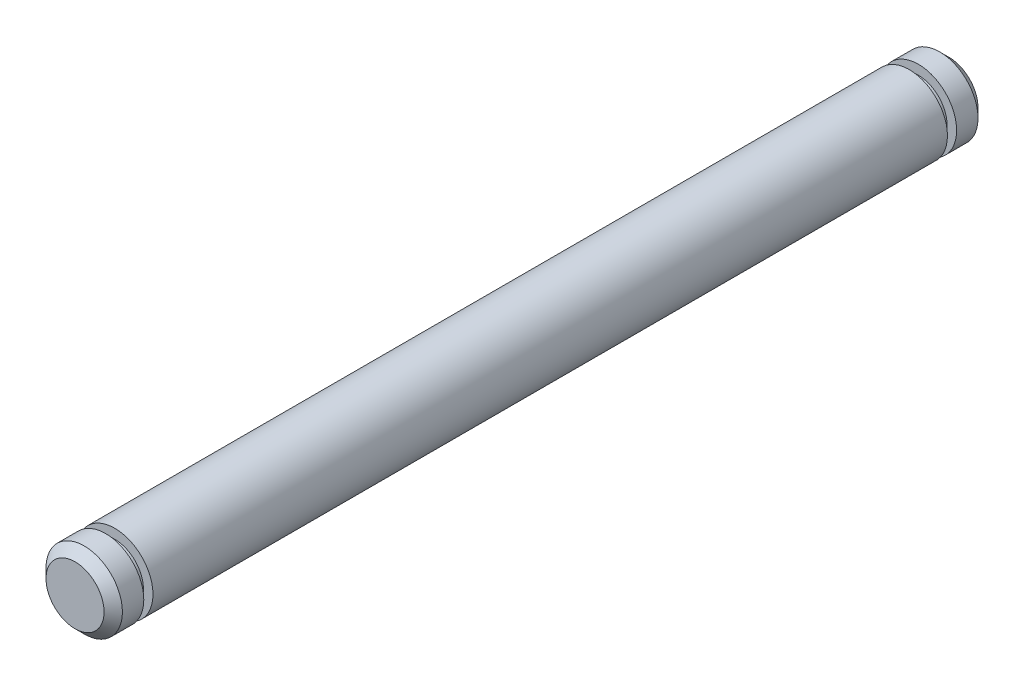
SolidWorks part; units mm, degrees
ref_plane "Front Plane" through (0, 0, 0) normal (0, 0, 1) x (1, 0, 0)
ref_plane "Top Plane" through (0, 0, 0) normal (0, 1, 0) x (1, 0, 0)
ref_plane "Right Plane" through (0, 0, 0) normal (1, 0, 0) x (0, 0, -1)
sketch "Sketch1" plane through (0, 0, 0) normal (0, 0, 1) x (1, 0, 0)
  circle A0 centre (0, 0) radius 1.5875
  dimension "D1" = 3.175
extrude "Boss-Extrude1" add sketch "Sketch1" along normal mid plane 33.0149
sketch "Sketch2" plane through (0, 0, 16.5075) normal (0, 0, 1) x (1, 0, 0)
  circle A0 centre (0, 0) radius 1.1913
  dimension "D1" = 2.3825
extrude "Boss-Extrude2" add sketch "Sketch2" along normal blind 0.381
sketch "Sketch3" plane through (0, 0, 16.8885) normal (0, 0, 1) x (1, 0, 0)
  circle A0 centre (0, 0) radius 1.5875 construction
  circle A1 centre (0, 0) radius 1.5875
extrude "Boss-Extrude3" add sketch "Sketch3" along normal blind 1.27
chamfer "Chamfer1" distance 0.381 1 edges at (1.5875, 0, 18.1585)
mirror "Mirror1" about plane through (0, 0, 0) normal (0, 0, 1) of "Boss-Extrude2", "Chamfer1", "Boss-Extrude3"
